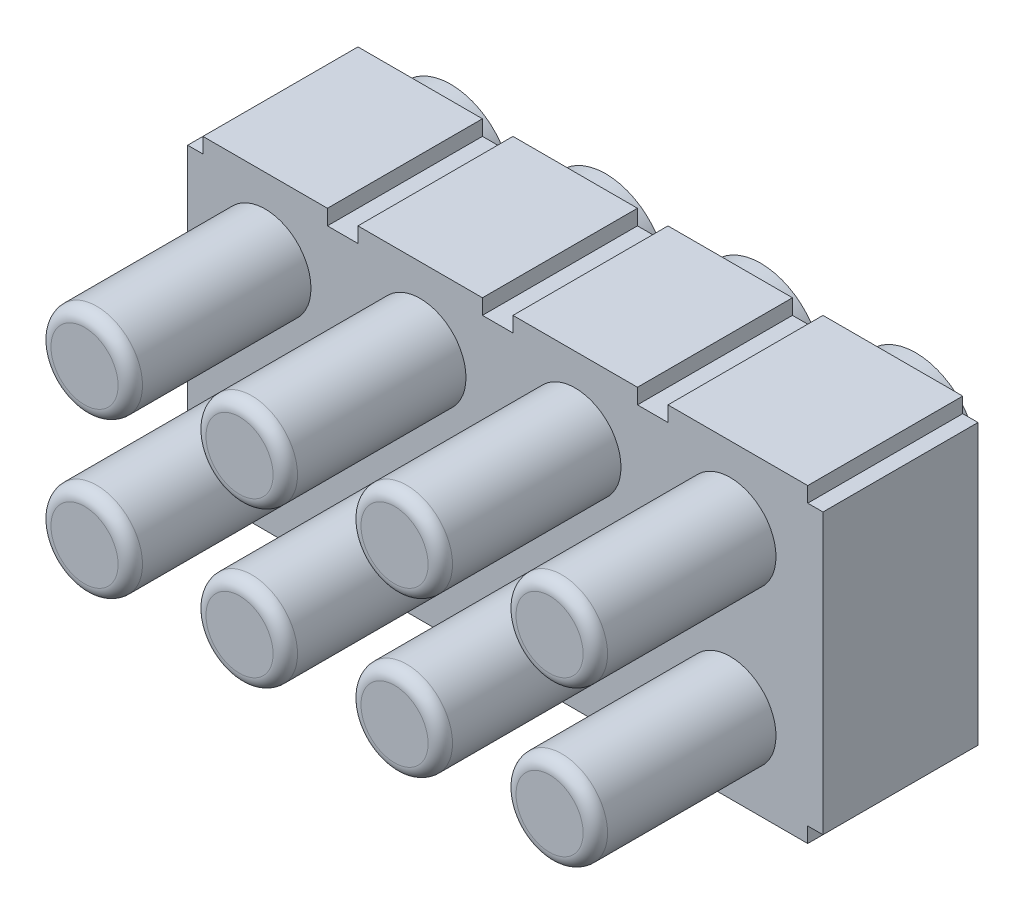
SolidWorks part; units mm, degrees
ref_plane "前视基准面" through (0, 0, 0) normal (0, 0, 1) x (1, 0, 0)
ref_plane "上视基准面" through (0, 0, 0) normal (0, 1, 0) x (1, 0, 0)
ref_plane "右视基准面" through (0, 0, 0) normal (1, 0, 0) x (0, 0, -1)
sketch "草图1" plane through (0, 0, 0) normal (0, 0, 1) x (1, 0, 0)
  line L0 (5.08, 2.29) -> (5.08, 2.54)
  line L1 (5.33, 0) -> (5.33, 2.29)
  line L2 (5.08, 2.54) -> (2.79, 2.54)
  line L3 (-5.08, 2.29) -> (-5.08, -2.29)
  line L4 (-4.83, -2.54) -> (-2.79, -2.54)
  line L5 (5.33, -2.29) -> (5.33, 0)
  line L7 (0.25, 2.54) -> (0.25, 2.29)
  line L8 (0.25, 2.29) -> (-0.25, 2.29)
  line L9 (-0.25, 2.29) -> (-0.25, 2.54)
  line L10 (-2.29, 2.54) -> (-2.29, 2.29)
  line L11 (-2.29, 2.29) -> (-2.79, 2.29)
  line L12 (-2.79, 2.29) -> (-2.79, 2.54)
  line L13 (-4.83, 2.54) -> (-4.83, 2.29)
  line L14 (-4.83, 2.29) -> (-5.08, 2.29)
  line L17 (2.79, 2.54) -> (2.79, 2.29)
  line L18 (2.79, 2.29) -> (2.29, 2.29)
  line L19 (2.29, 2.29) -> (2.29, 2.54)
  line L20 (2.29, 2.54) -> (0.25, 2.54)
  line L21 (5.33, 2.29) -> (5.08, 2.29)
  line L23 (0.25, 2.54) -> (2.29, 2.54) construction
  line L24 (2.79, -2.54) -> (5.08, -2.54)
  line L25 (0.25, -2.54) -> (2.29, -2.54)
  line L26 (5.33, -2.29) -> (5.08, -2.29)
  line L27 (5.08, -2.29) -> (5.08, -2.54)
  line L28 (2.79, -2.54) -> (2.79, -2.29)
  line L29 (2.79, -2.29) -> (2.29, -2.29)
  line L30 (2.29, -2.29) -> (2.29, -2.54)
  line L31 (0.25, -2.54) -> (0.25, -2.29)
  line L32 (0.25, -2.29) -> (-0.25, -2.29)
  line L33 (-0.25, -2.29) -> (-0.25, -2.54)
  line L34 (-2.29, -2.54) -> (-2.29, -2.29)
  line L35 (-2.29, -2.29) -> (-2.79, -2.29)
  line L36 (-2.79, -2.29) -> (-2.79, -2.54)
  line L37 (-4.83, -2.54) -> (-4.83, -2.29)
  line L39 (-4.83, -2.29) -> (-5.08, -2.29)
  line L40 (-2.29, -2.54) -> (-0.25, -2.54)
  line L41 (5.33, 2.54) -> (5.33, 2.29) [skipped]
  line L42 (-2.79, 2.54) -> (-4.83, 2.54)
  line L43 (-0.25, 2.54) -> (-2.29, 2.54)
  line L44 (-0.25, 2.54) -> (-2.29, 2.54) construction
  line L45 (-5.33, 2.29) -> (-5.33, 2.54) [skipped]
  line L46 (4.83, 2.29) -> (4.83, 2.54) [skipped]
  dimension "D1" = 3
  dimension "D3" = 3
extrude "凸台-拉伸1" add sketch "草图1" along normal blind 2.54
sketch "草图2" plane through (0, 0, 0) normal (0, 0, -1) x (-1, 0, 0)
  circle A0 centre (-1.27, 1.27) radius 1
  circle A1 centre (1.27, 1.27) radius 1
  circle A2 centre (3.81, 1.27) radius 1
  circle A3 centre (1.27, -1.27) radius 1
  circle A4 centre (3.81, -1.27) radius 1
  circle A5 centre (-1.27, -1.27) radius 1
  circle A6 centre (-3.81, 1.27) radius 1
  circle A7 centre (-3.81, -1.27) radius 1
  dimension "D1" = 3
  dimension "D2" = 2
extrude "凸台-拉伸2" add sketch "草图2" along normal blind 0.5
sketch "草图3" plane through (0, 0, -0.5) normal (0, 0, -1) x (-1, 0, 0)
  circle A0 centre (-3.81, 1.27) radius 0.75
  circle A1 centre (-1.27, 1.27) radius 0.75
  circle A2 centre (1.27, 1.27) radius 0.75
  circle A3 centre (3.81, 1.27) radius 0.75
  circle A4 centre (-1.27, -1.27) radius 0.75
  circle A5 centre (1.27, -1.27) radius 0.75
  circle A6 centre (3.81, -1.27) radius 0.75
  circle A7 centre (-3.81, -1.27) radius 0.75
  dimension "D1" = 4
  dimension "D2" = 2
extrude "凸台-拉伸3" add sketch "草图3" against normal blind 8
sketch "草图4" plane through (0, 0, 7.5) normal (0, 0, 1) x (1, 0, 0)
  circle A0 centre (-3.81, 1.27) radius 0.45
  circle A1 centre (-1.27, 1.27) radius 0.45
  circle A2 centre (1.27, 1.27) radius 0.45
  circle A3 centre (3.81, 1.27) radius 0.45
  circle A4 centre (-1.27, -1.27) radius 0.45
  circle A5 centre (1.27, -1.27) radius 0.45
  circle A6 centre (3.81, -1.27) radius 0.45
  circle A7 centre (-3.81, -1.27) radius 0.45
  dimension "D1" = 4
  dimension "D2" = 2
extrude "凸台-拉伸4" add sketch "草图4" along normal blind 2
fillet "圆角1" radius 0.4 8 edges at (4.26, 1.27, 9.5) (-3.36, -1.27, 9.5) (-3.36, 1.27, 9.5) (-0.82, 1.27, 9.5) (-0.82, -1.27, 9.5) (1.72, -1.27, 9.5) (1.72, 1.27, 9.5) (4.26, -1.27, 9.5)
fillet "圆角2" radius 0.2 8 edges at (-4.56, 1.27, 7.5) (-2.02, -1.27, 7.5) (-2.02, 1.27, 7.5) (0.52, 1.27, 7.5) (0.52, -1.27, 7.5) (3.06, 1.27, 7.5) (3.06, -1.27, 7.5) (-4.56, -1.27, 7.5)
sketch "草图5" plane through (0, 0, -0.5) normal (0, 0, -1) x (-1, 0, 0)
  circle A0 centre (0, 0) radius 0.6261
sketch "草图6" plane through (0, 0, 9.5) normal (0, 0, 1) x (1, 0, 0)
  circle A0 centre (0, 0) radius 7.8181
extrude "切除-拉伸1" cut sketch "草图6" against normal blind 4
fillet "圆角3" radius 0.2 8 edges at (-3.06, -1.27, 5.5) (2.02, 1.27, 5.5) (-3.06, 1.27, 5.5) (-0.52, -1.27, 5.5) (-0.52, 1.27, 5.5) (2.02, -1.27, 5.5) (4.56, -1.27, 5.5) (4.56, 1.27, 5.5)
